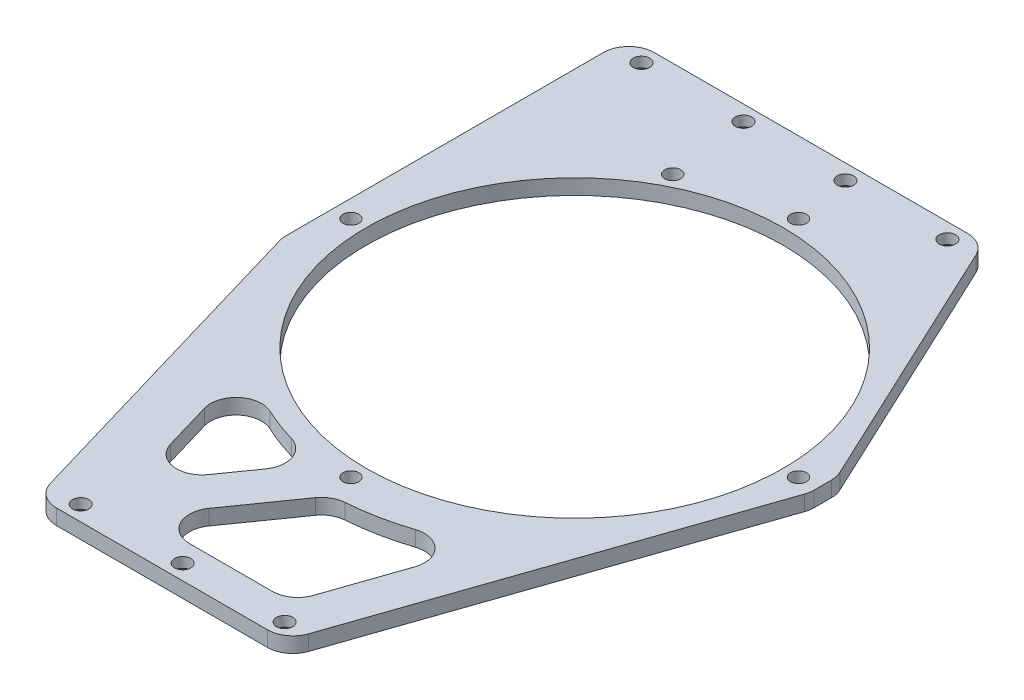
SolidWorks part; units mm, degrees
material "Thornel Mat VMA"
ref_plane "前视基准面" through (0, 0, 0) normal (0, 0, 1) x (1, 0, 0)
ref_plane "上视基准面" through (0, 0, 0) normal (0, 1, 0) x (1, 0, 0)
ref_plane "右视基准面" through (0, 0, 0) normal (1, 0, 0) x (0, 0, -1)
sketch "草图1" plane through (0, 0, 0) normal (0, 1, 0) x (1, 0, 0)
  line L0 (-31.9, 0) -> (-31.9, 46.9) construction
  line L3 (-112.38, 58) -> (47.62, 58)
  line L4 (-112.38, 58) -> (-112.38, -78)
  line L5 (-112.38, -78) -> (47.62, -78)
  line L6 (47.62, 58) -> (47.62, -78)
  line L7 (47.62, -10) -> (-112.38, -10) construction
  line L8 (-32.38, -78) -> (-32.38, 58) construction
  circle A0 centre (0, 0) radius 40.9
  circle A1 centre (0, 0) radius 43.9 construction
  circle A2 centre (0, 0) radius 31.9 construction
  circle A4 centre (0, 0) radius 40.9 construction
  circle A5 centre (0, 43.9) radius 1.55
  circle A6 centre (43.9, 0) radius 1.55
  circle A7 centre (0, -43.9) radius 1.55
  circle A8 centre (-43.9, 0) radius 1.55
  arc A9 (2.9681, 44.336) -> (-2.9681, 44.336) centre (0, 43.9) ccw construction
  arc A10 (44.336, -2.9681) -> (44.336, 2.9681) centre (43.9, 0) ccw construction
  arc A11 (-2.9681, -44.336) -> (2.9681, -44.336) centre (0, -43.9) ccw construction
  arc A12 (-44.336, 2.9681) -> (-44.336, -2.9681) centre (-43.9, 0) ccw construction
  arc A14 (-42.6388, -4.7266) -> (-4.7266, -42.6388) centre (0, 0) ccw construction
  arc A15 (4.7266, -42.6388) -> (42.6388, -4.7266) centre (0, 0) ccw construction
  arc A16 (42.6388, 4.7266) -> (4.7266, 42.6388) centre (0, 0) ccw construction
  arc A17 (-4.7266, 42.6388) -> (-15.1153, 40.149) centre (0, 0) ccw construction
  circle A18 centre (-19.9, 39.1306) radius 1.55
  arc A22 (-44.336, -2.9681) -> (-42.6388, -4.7266) centre (-44.6267, -4.9469) cw construction
  arc A24 (2.9681, -44.336) -> (4.7266, -42.6388) centre (4.9469, -44.6267) cw construction
  arc A25 (-2.9681, -44.336) -> (-4.7266, -42.6388) centre (-4.9469, -44.6267) ccw construction
  arc A26 (44.336, -2.9681) -> (42.6388, -4.7266) centre (44.6267, -4.9469) ccw construction
  arc A27 (44.336, 2.9681) -> (42.6388, 4.7266) centre (44.6267, 4.9469) cw construction
  arc A28 (2.9681, 44.336) -> (4.7266, 42.6388) centre (4.9469, 44.6267) ccw construction
  arc A29 (-4.7266, 42.6388) -> (-2.9681, 44.336) centre (-4.9469, 44.6267) ccw construction
  arc A30 (-17.452, 40.8646) -> (-22.7433, 38.1737) centre (-19.9, 39.1306) ccw construction
  arc A32 (-23.5414, 35.8638) -> (-42.6388, 4.7266) centre (0, 0) ccw construction
  arc A33 (-17.452, 40.8646) -> (-15.1153, 40.149) centre (-15.8199, 42.0207) ccw construction
  arc A34 (-22.7433, 38.1737) -> (-23.5414, 35.8638) centre (-24.6389, 37.5358) cw construction
  arc A35 (-44.336, 2.9681) -> (-42.6388, 4.7266) centre (-44.6267, 4.9469) ccw construction
  circle A37 centre (44.62, 55) radius 1.6 construction
  circle A38 centre (44.62, 35) radius 1.6 construction
  circle A39 centre (44.62, -75) radius 1.6 construction
  circle A40 centre (44.62, -55) radius 1.6 construction
  circle A41 centre (18.1, 55) radius 1.6
  circle A42 centre (-1.9, 55) radius 1.6
  circle A45 centre (-21.9, 55) radius 1.6
  circle A46 centre (-41.9, 55) radius 1.6
  circle A47 centre (18.1, -75) radius 1.6
  circle A48 centre (-1.9, -75) radius 1.6
  circle A49 centre (-21.9, -75) radius 1.6
  circle A50 centre (-41.9, -75) radius 1.6
  circle A51 centre (39.0795, -20) radius 1.55 construction
  point P11 (0, 46.9)
  point P34 (-21.8963, 36.8912)
  point P52 (2.7945, -42.8089)
  point P59 (42.8089, 2.7945)
  dimension "D1" = 81.8
  dimension "D3" = 9
  dimension "D6" = 3.1
  dimension "D8" = 6
  dimension "D12" = 2
  dimension "D13" = 136
  dimension "D9" = 2
  dimension "D10" = 160
  dimension "D17" = 3.2
  dimension "D24" = 20
  dimension "D5" = 12
  dimension "D11" = 58
  dimension "D14" = 112.38
  dimension "D15" = 45
  dimension "D16" = 20
  dimension "D18" = 3
  dimension "D19" = 20
  dimension "D20" = 30.48
  dimension "D21" = 3
  dimension "D23" = 40
  dimension "D2" = 3
  dimension "D4" = 4
  dimension "D22" = 2
  dimension "D7" = 4
extrude "凸台-拉伸1" add sketch "草图1" along normal blind 3
sketch "草图2" plane through (0, 0, 0) normal (0, 1, 0) x (1, 0, 0)
  line L0 (-112.38, -78) -> (47.62, -78) construction
  line L1 (-112.38, 58) -> (-137.38, 58)
  line L2 (-112.38, 58) -> (-112.38, -78)
  line L3 (-112.38, -78) -> (-137.38, -78)
  line L4 (-137.38, 58) -> (-137.38, -78)
  dimension "D1" = 25
extrude "凸台-拉伸2" add sketch "草图2" along normal blind 3
sketch "草图3" plane through (0, 3, 0) normal (0, 1, 0) x (1, 0, 0)
  line L0 (-137.38, -78) -> (47.62, -78) construction
  line L1 (-137.38, 58) -> (-47.38, 58)
  line L2 (-137.38, 58) -> (-137.38, -78)
  line L3 (-137.38, -78) -> (-47.38, -78)
  line L4 (-47.38, 58) -> (-47.38, -78)
  dimension "D1" = 90
extrude "切除-拉伸1" cut sketch "草图3" against normal through all
sketch "草图4" plane through (0, 0, 0) normal (0, 1, 0) x (1, 0, 0)
  line L0 (18.1, 55) -> (43.9, 0) construction
  line L1 (43.9, 0) -> (18.1, -75) construction
  line L2 (47.62, 58) -> (47.62, 3.8431)
  line L3 (47.62, -78) -> (47.62, 58) construction
  line L4 (47.62, 3.8431) -> (22.2155, 58)
  line L5 (47.62, 58) -> (-47.38, 58) construction
  line L6 (22.2155, 58) -> (47.62, 58)
  line L7 (47.62, -1.4827) -> (47.62, -78)
  line L8 (47.62, -78) -> (21.2981, -78)
  line L9 (-47.38, -78) -> (47.62, -78) construction
  line L10 (21.2981, -78) -> (47.62, -1.4827)
  line L11 (-43.9, 0) -> (-40.7809, -3.1191) construction
  line L12 (0, -43.9) -> (-21.9, -75) construction
  line L13 (-21.9, -75) -> (-43.9, 0) construction
  line L14 (-3.1191, -40.7809) -> (0, -43.9) construction
  line L15 (-20.3959, -65.9166) -> (-29.908, -33.4891)
  line L17 (-20.3959, -65.9166) -> (-5.3695, -44.5778)
  line L18 (33.6893, -29.6824) -> (18.1, -75) construction
  line L19 (-5.3695, -44.5778) -> (-5.3695, -44.5778) construction
  line L20 (-20.3959, -65.9166) -> (-29.908, -33.4891) construction
  line L21 (-29.908, -33.4891) -> (-29.908, -33.4891) construction
  line L22 (-5.3695, -44.5778) -> (-20.3959, -65.9166) construction
  line L23 (18.1, -75) -> (-21.9, -75) construction
  line L24 (-21.9, -75) -> (-0.7003, -44.8945) construction
  line L25 (-14.191, -71) -> (1.3851, -48.8804)
  line L26 (25.2682, -41.8656) -> (15.2459, -71)
  line L27 (15.2459, -71) -> (-14.191, -71)
  line L28 (-47.38, -78) -> (-47.38, -26)
  line L29 (-47.38, -78) -> (-47.38, 58) construction
  line L31 (-27.38, -78) -> (-47.38, -78)
  line L33 (-47.38, -10) -> (-47.38, -26)
  line L34 (-27.38, -78) -> (-47.38, -10)
  circle A0 centre (0, 0) radius 40.9 construction
  arc A1 (-40.7809, -3.1191) -> (-3.1191, -40.7809) centre (0, 0) ccw construction
  arc A2 (40.0819, 8.1393) -> (31.8825, 25.6186) centre (0, 0) ccw construction
  arc A3 (-3.1191, -40.7809) -> (-40.7809, -3.1191) centre (0, 0) cw construction
  arc A4 (-29.908, -33.4891) -> (-5.3695, -44.5778) centre (0, 0) ccw
  circle A5 centre (-21.9, -75) radius 1.6 construction
  arc A6 (-0.7003, -44.8945) -> (33.6893, -29.6824) centre (0, 0) ccw construction
  circle A7 centre (0, 0) radius 44.9
  circle A8 centre (0, 0) radius 44.9 construction
  arc A9 (1.3851, -48.8804) -> (25.2682, -41.8656) centre (0, 0) ccw
  dimension "D3" = 4
  dimension "D5" = 4
  dimension "D1" = 5
  dimension "D2" = 4
  dimension "D4" = 4
  dimension "D6" = 52
  dimension "D7" = 20
extrude "切除-拉伸3" cut sketch "草图4" along normal through all
fillet "圆角1" radius 5 7 edges at (47.62, 1.5, 1.4827) (21.2981, 1.5, 78) (-47.38, 1.5, -58) (22.2155, 1.5, -58) (47.62, 1.5, -3.8431) (-27.38, 1.5, 78) (-47.38, 1.5, 10)
fillet "圆角2" radius 5 7 edges at (1.3851, 1.5, 48.8804) (-14.191, 1.5, 71) (15.2459, 1.5, 71) (-20.3959, 1.5, 65.9166) (-5.3695, 1.5, 44.5778) (-29.908, 1.5, 33.4891) (25.2682, 1.5, 41.8656)
chamfer "倒角1" distance 1 angle 45 7 edges at (18.1, 0, 73.4) (-1.9, 0, 73.4) (-21.9, 0, 73.4) (-41.9, 0, -53.4) (-21.9, 0, -53.4) (-1.9, 0, -53.4) (18.1, 0, -53.4)
